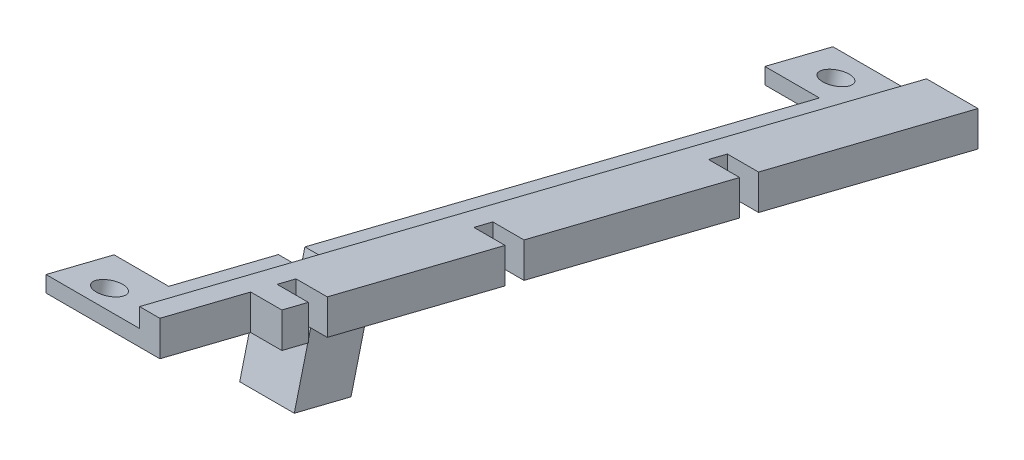
SolidWorks part; units mm, degrees
ref_plane "Front Plane" through (0, 0, 0) normal (0, 0, 1) x (1, 0, 0)
ref_plane "Top Plane" through (0, 0, 0) normal (0, 1, 0) x (1, 0, 0)
ref_plane "Right Plane" through (0, 0, 0) normal (1, 0, 0) x (0, 0, -1)
sketch "Sketch1" plane through (0, 0, 0) normal (1, 0, 0) x (0, 0, -1)
  line L0 (0, 0) -> (117.1645, 0) construction
  line L1 (0, 0) -> (89.2672, -22.2568)
  line L2 (0, 0) -> (0, -4.5)
  line L3 (0, -4.5) -> (89.2672, -26.7568)
  line L4 (89.2672, -26.7568) -> (89.2672, -22.2568)
  line L5 (61.1286, -19.7411) -> (61.1286, -15.2411)
  line L6 (58.7029, -19.1363) -> (58.7029, -14.6363)
  line L7 (31.0495, -12.2415) -> (31.0495, -7.7415)
  line L8 (28.6237, -11.6367) -> (28.6237, -7.1367)
  line L9 (5.8218, -5.9515) -> (5.8218, -1.4515)
  line L10 (3.396, -5.3467) -> (3.396, -0.8467)
  dimension "D1" = 14
  dimension "D2" = 29
  dimension "D3" = 31.5
  dimension "D4" = 60
  dimension "D5" = 62.5
  dimension "D6" = 86
  dimension "D7" = 88.5
  dimension "D8" = 92
  dimension "D9" = 4.5
extrude "Side comb" add sketch "Sketch1" along normal blind 4 contours L3 L10 L1 L2 | L9 L3 L8 L1 | L7 L3 L6 L1 | L5 L3 L4 L1
sketch "Sketch2" plane through (0, 0, 0) normal (-1, 0, 0) x (0, 0, 1)
  line L1 (-89.2672, -22.2568) -> (-89.2672, -26.7568)
  line L4 (-89.2672, -22.2568) -> (11.6435, 2.9031)
  line L5 (0, 0) -> (0, -4.5) construction
  line L6 (-89.2672, -26.7568) -> (11.6435, -1.5969)
  line L7 (11.6435, 2.9031) -> (11.6435, -1.5969)
  dimension "D1" = 12
extrude "Side spacer" add sketch "Sketch2" along normal blind 2.6
sketch "Sketch3" plane through (-2.6, 0, 0) normal (-1, 0, 0) x (0, 0, 1)
  line L0 (-89.2672, -24.6956) -> (11.6435, 0.4643)
  line L1 (-89.2672, -22.2568) -> (-89.2672, -26.7568) construction
  line L2 (11.6435, -1.5969) -> (11.6435, 2.9031) construction
  line L3 (-89.2672, -26.7568) -> (11.6435, -1.5969) construction
  line L4 (-89.2672, -24.6956) -> (-89.2672, -26.7568)
  line L5 (-89.2672, -26.7568) -> (11.6435, -1.5969)
  line L6 (11.6435, -1.5969) -> (11.6435, 0.4643)
  dimension "D1" = 2
extrude "Narrow support" add sketch "Sketch3" along normal blind 5
sketch "Sketch4" plane through (-7.6, 0, 0) normal (-1, 0, 0) x (0, 0, 1)
  line L0 (-89.2672, -24.6956) -> (-80.5345, -22.5183)
  line L1 (11.6435, 0.4643) -> (-89.2672, -24.6956) construction
  line L2 (-80.5345, -22.5183) -> (-80.5345, -24.5795)
  line L3 (-89.2672, -26.7568) -> (11.6435, -1.5969) construction
  line L4 (-80.5345, -24.5795) -> (-89.2672, -26.7568)
  line L5 (-89.2672, -26.7568) -> (-89.2672, -24.6956)
  line L6 (11.6435, 0.4643) -> (11.6435, -1.5969)
  line L7 (11.6435, -1.5969) -> (2.9109, -3.7742)
  line L8 (2.9109, -3.7742) -> (2.9109, -1.713)
  line L9 (11.6435, 0.4643) -> (-89.2672, -24.6956) construction
  line L10 (2.9109, -1.713) -> (11.6435, 0.4643)
  dimension "D1" = 9
  dimension "D2" = 9
extrude "Screw tabs" add sketch "Sketch4" along normal blind 7
sketch "Sketch5" plane through (0, -2.296, 0.5725) normal (0, 0.9703, -0.2419) x (1, 0, 0)
  line L0 (-2.6, -11.41) -> (-2.6, 92.59) construction
  line L1 (-14.6, 92.59) -> (-2.6, 92.59) construction
  line L2 (-2.6, 12.09) -> (-7.6, 12.09) construction
  line L3 (-7.6, -2.41) -> (-7.6, 83.59) construction
  line L4 (-9.85, 88.09) -> (-2.6, 88.09) construction
  line L5 (-9.85, -7.91) -> (-2.6, -7.91) construction
  circle A0 centre (-9.85, 88.09) radius 1.75
  circle A1 centre (-9.85, -7.91) radius 1.75
  dimension "D4" = 3.5
  dimension "D1" = 7.25
  dimension "D2" = 100.5
  dimension "D5" = 76
  dimension "D6" = 4.5
extrude "Screw holes" cut sketch "Sketch5" against normal blind 7
sketch "Sketch6" plane through (0, -4.2366, 1.0563) normal (0, -0.9703, 0.2419) x (1, 0, 0)
  line L2 (-2.6, -12.09) -> (-7.6, -12.09) construction
  line L3 (-2.6, -12.09) -> (-7.6, -12.09)
  line L4 (-2.6, -15.59) -> (-7.6, -15.59)
  line L5 (-7.6, -84.0886) -> (-7.6, 1.9114) construction
  line L6 (-7.6, -15.59) -> (-7.6, -17.59)
  line L7 (-7.6, -17.59) -> (-0.6, -17.59)
  line L8 (-0.6, -10.09) -> (-0.6, -17.59)
  line L9 (-0.6, -10.09) -> (-7.6, -10.09)
  line L10 (-7.6, -10.09) -> (-7.6, -12.09)
  line L11 (-2.6, -15.59) -> (-2.6, -12.09)
  dimension "D1" = 2
  dimension "D2" = 2
  dimension "D4" = 3.5
sketch "Sketch7" plane through (0, -4.2366, 1.0563) normal (0, -0.9703, 0.2419) x (1, 0, 0)
  line L0 (-7.6, -12.09) -> (-7.6, -15.59)
  line L1 (-7.6, -15.59) -> (-2.6, -15.59)
  line L2 (-2.6, -15.59) -> (-2.6, -12.09)
  line L3 (-2.6, -12.09) -> (-7.6, -12.09)
extrude "Gap for support bar" cut sketch "Sketch7" against normal up to vertex (2 mm away)
extrude "Support bar sides" add sketch "Sketch6" along normal blind 8.5
sketch "Sketch8" plane through (0, -12.4841, 3.1126) normal (0, -0.9703, 0.2419) x (1, 0, 0)
  line L0 (-0.6, -17.59) -> (-0.6, -10.09) construction
  line L1 (-7.6, -10.09) -> (-0.6, -10.09)
  line L2 (-7.6, -10.09) -> (-7.6, -17.59)
  line L3 (-7.6, -17.59) -> (-0.6, -17.59)
  line L4 (-0.6, -10.09) -> (-0.6, -17.59)
extrude "Support bar bottom" add sketch "Sketch8" along normal blind 2
